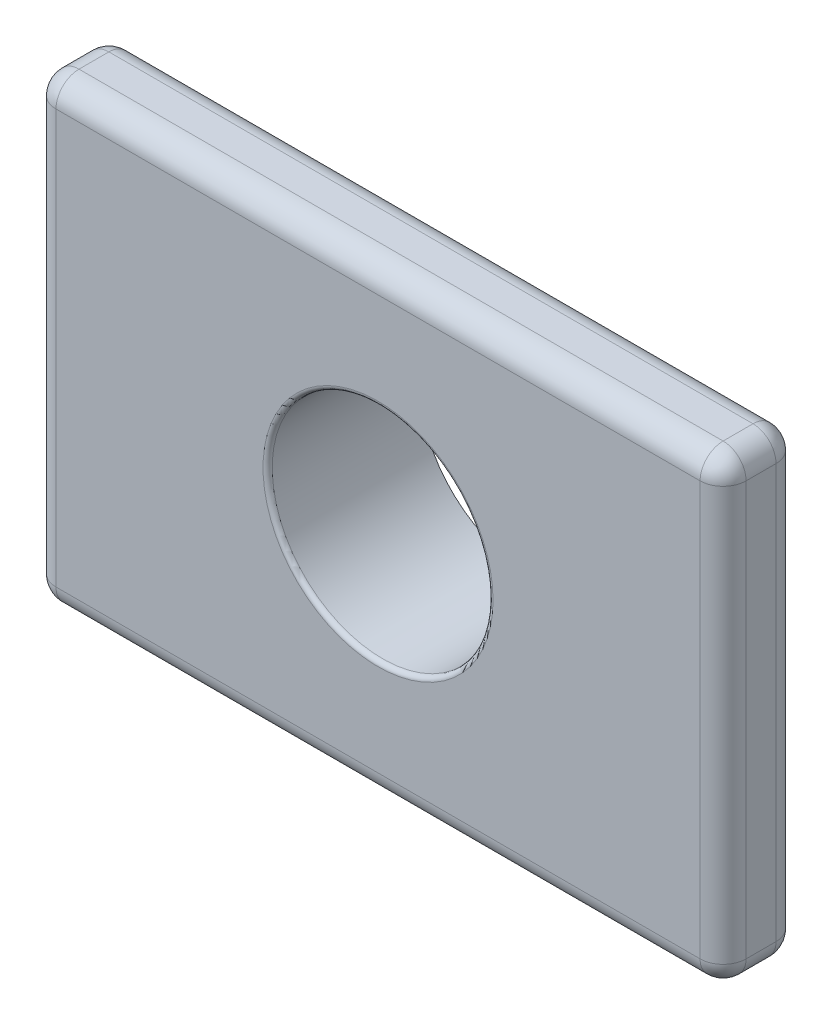
SolidWorks part; units mm, degrees
ref_plane "Front Plane" through (0, 0, 0) normal (0, 0, 1) x (1, 0, 0)
ref_plane "Top Plane" through (0, 0, 0) normal (0, 1, 0) x (1, 0, 0)
ref_plane "Right Plane" through (0, 0, 0) normal (1, 0, 0) x (0, 0, -1)
sketch "Sketch1" plane through (0, 0, 0) normal (0, 0, 1) x (1, 0, 0)
  line L0 (0, 9.998) -> (15, 0) construction
  line L1 (0, 0) -> (15, 0)
  line L2 (0, 0) -> (0, 9.998)
  line L3 (0, 9.998) -> (15, 9.998)
  line L4 (15, 0) -> (15, 9.998)
  line L5 (15, 9.998) -> (0, 0) construction
  circle A0 centre (7.5, 4.999) radius 2.4
  dimension "D3" = 4.8
  dimension "D1" = 15
  dimension "D2" = 9.998
extrude "Boss-Extrude1" add sketch "Sketch1" along normal blind 1.65 contours L2 L3 L4 L1
sketch "Sketch2" plane through (0, 0, 0) normal (0, 0, -1) x (-1, 0, 0)
  circle A2 centre (-7.5, 4.999) radius 2.6
  circle A3 centre (-7.5, 4.999) radius 2.6
  dimension "D1" = 0.2
extrude "Boss-Extrude2" add sketch "Sketch2" along normal blind 1.65
sketch "Sketch3" plane through (0, 0, 1.65) normal (0, 0, 1) x (1, 0, 0)
  circle A0 centre (7.5, 4.999) radius 2.4 construction
  circle A1 centre (7.5, 4.999) radius 2.4
extrude "Cut-Extrude1" cut sketch "Sketch3" against normal through all
fillet "Fillet1" radius 0.1 3 edges at (9.9, 4.999, 1.65) (4.9, 4.999, -1.65) (10.1, 4.999, 0)
fillet "Fillet3" radius 0.5 4 edges at (15, 9.998, 0.825) (15, 0, 0.825) (0, 9.998, 0.825) (0, 0, 0.825)
fillet "Fillet4" radius 0.5 16 edges at (14.8536, 0.1464, 1.65) (7.5, 0, 1.65) (0.1464, 0.1464, 1.65) (0, 4.999, 1.65) (0.1464, 9.8516, 1.65) (7.5, 9.998, 1.65) (14.8536, 9.8516, 1.65) (14.8536, 0.1464, 0) (7.5, 0, 0) (0.1464, 0.1464, 0) (0, 4.999, 0) (0.1464, 9.8516, 0) (7.5, 9.998, 0) (14.8536, 9.8516, 0) (15, 4.999, 1.65) (15, 4.999, 0)
